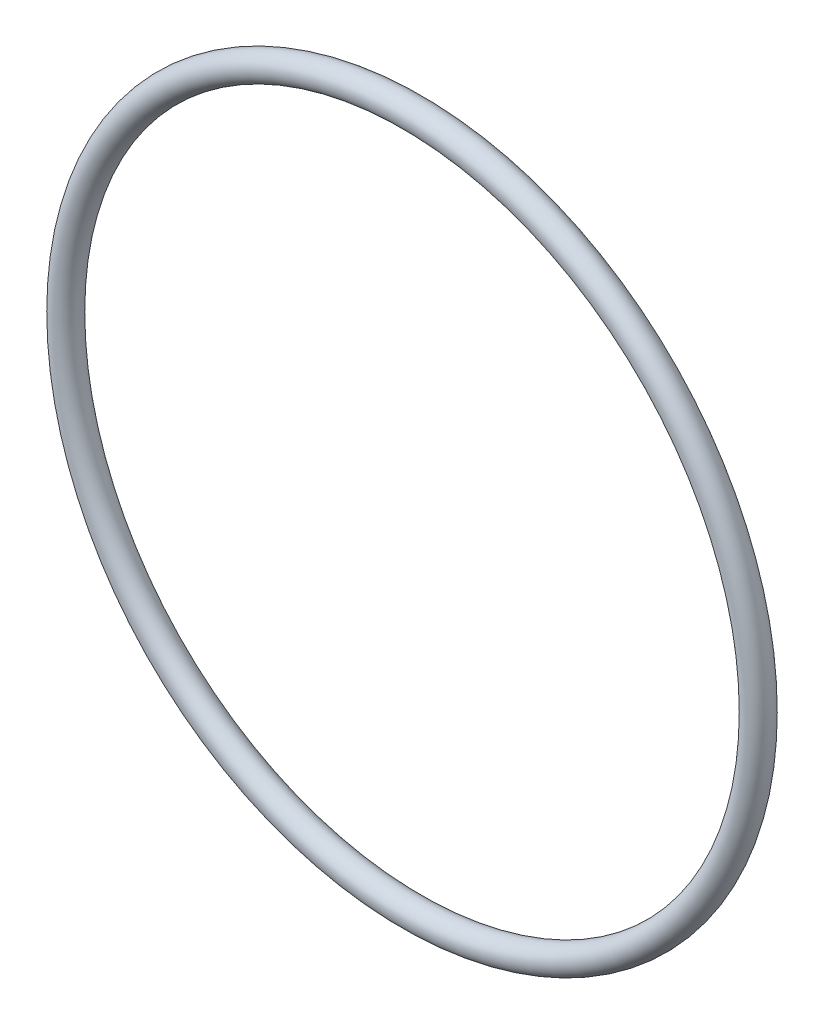
SolidWorks part; units mm, degrees
material "High Temp Silicon"
ref_plane "Front" through (0, 0, 0) normal (0, 0, 1) x (1, 0, 0)
ref_plane "Top" through (0, 0, 0) normal (0, 1, 0) x (1, 0, 0)
ref_plane "Right" through (0, 0, 0) normal (1, 0, 0) x (0, 0, -1)
sketch "Sketch1" plane through (0, 0, 0) normal (1, 0, 0) x (0, -1, 0)
  line L0 (-32.385, 0) -> (32.385, 0) construction
  line L1 (32.385, 0) -> (33.6931, 0) construction
  line L2 (0, 0) -> (0, 4.6196) construction
  circle A0 centre (33.6931, 0) radius 1.3081
  point P3 (0, 0)
  dimension "D1" = 64.77
  dimension "D2" = 2.6162
revolve "Revolve1" add sketch "Sketch1" angle 360 about L2
sketch "Sketch2" plane through (0, 0, 0) normal (0, 0, 1) x (1, 0, 0)
  circle A0 centre (0, 0) radius 32.385 construction
